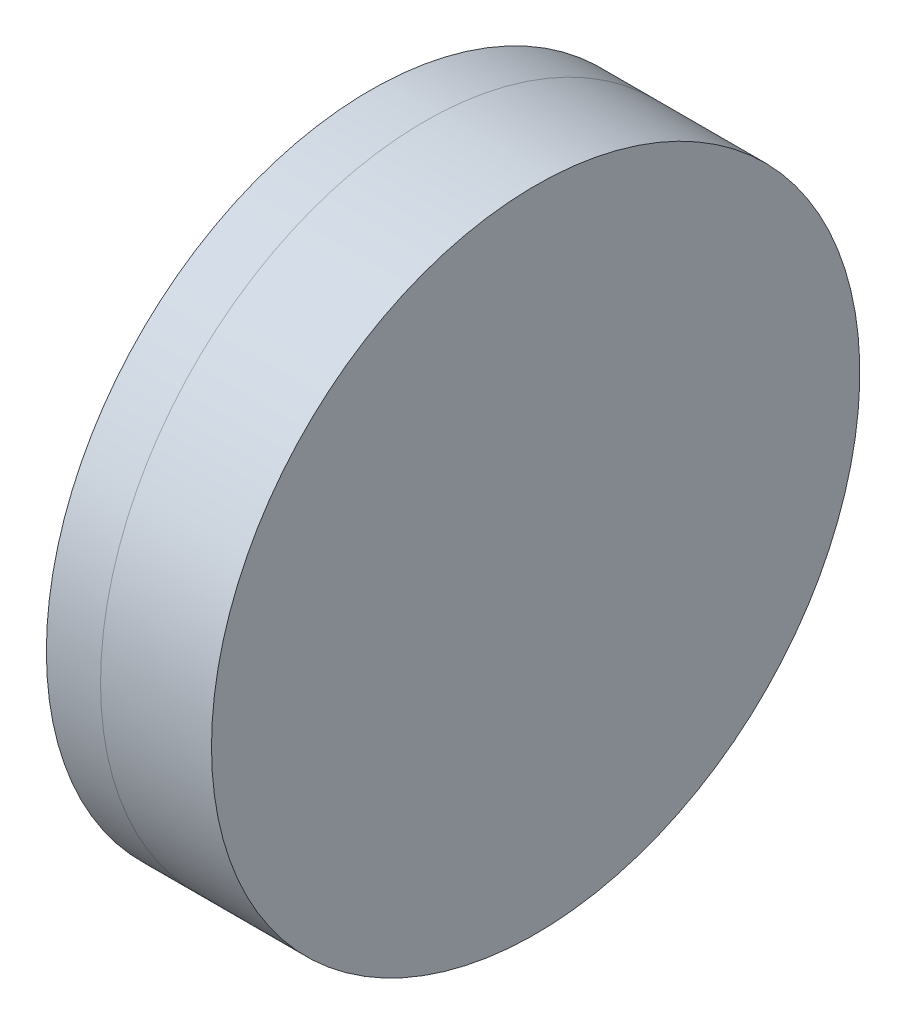
SolidWorks part; units mm, degrees
ref_plane "前视基准面" through (0, 0, 0) normal (0, 0, 1) x (1, 0, 0)
ref_plane "上视基准面" through (0, 0, 0) normal (0, 1, 0) x (1, 0, 0)
ref_plane "右视基准面" through (0, 0, 0) normal (1, 0, 0) x (0, 0, -1)
sketch "草图1" plane through (0, 0, 0) normal (0, 1, 0) x (1, 0, 0)
  line L0 (124.5233, 0) -> (646.9917, 0) construction
  line L1 (336.3004, -12.7) -> (338.4227, -12.7)
  line L2 (336.3004, 12.7) -> (338.4227, 12.7)
  arc A0 (338.4227, -12.7) -> (338.4227, 12.7) centre (250.0001, 0) ccw
  arc A1 (336.3004, 12.7) -> (336.3004, -12.7) centre (418.9301, 0) ccw
  point P10 (335.3301, 0)
  point P11 (339.3301, 0)
  dimension "D3" = 83.6
  dimension "D4" = 89.33
  dimension "D1" = 12.7
  dimension "D2" = 12.7
  dimension "D5" = 4
revolve "旋转1" add sketch "草图1" angle 360 about L0
sketch "草图2" plane through (0, 0, 0) normal (0, 1, 0) x (1, 0, 0)
  line L0 (-0.5519, 0) -> (622.6607, 0) construction
  line L2 (338.4227, 12.7) -> (342.7695, 12.7)
  line L3 (338.4227, -12.7) -> (342.7695, -12.7)
  arc A0 (342.7695, -12.7) -> (342.7695, 12.7) centre (-987.6699, 0) ccw
  arc A1 (338.4227, -12.7) -> (338.4227, 12.7) centre (250.0001, 0) ccw construction
  arc A2 (338.4227, -12.7) -> (338.4227, 12.7) centre (250.0001, 0) ccw
  point P4 (339.3301, 0)
  point P8 (342.8301, 0)
  dimension "D1" = 1330.5
  dimension "D2" = 3.5
revolve "旋转3" add sketch "草图2" angle 360 about L0
